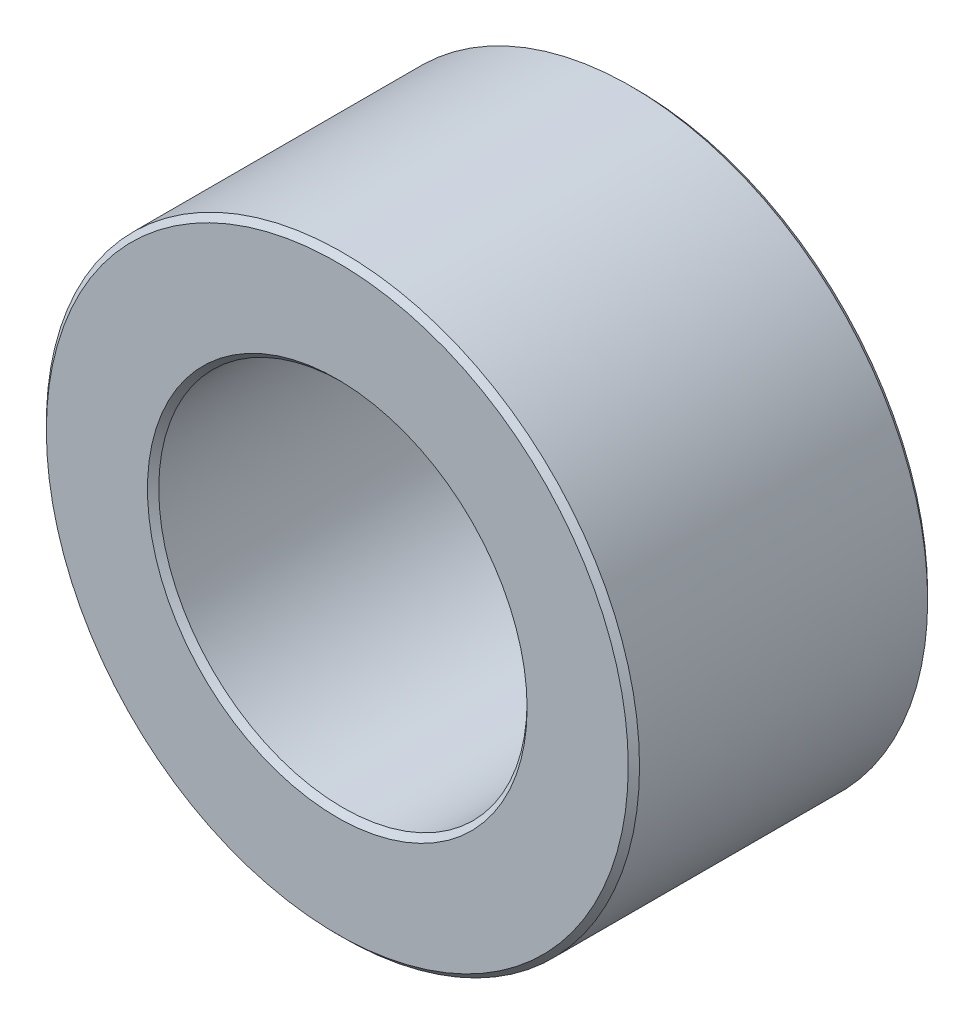
SolidWorks part; units mm, degrees
ref_plane "Front Plane" through (0, 0, 0) normal (0, 0, 1) x (1, 0, 0)
ref_plane "Top Plane" through (0, 0, 0) normal (0, 1, 0) x (1, 0, 0)
ref_plane "Right Plane" through (0, 0, 0) normal (1, 0, 0) x (0, 0, -1)
sketch "Sketch1" plane through (0, 0, 0) normal (0, 0, 1) x (1, 0, 0)
  circle A0 centre (0, 0) radius 52.5
  circle A1 centre (0, 0) radius 32.6
  dimension "D1" = 105
  dimension "D2" = 65.2
extrude "Boss-Extrude1" add sketch "Sketch1" along normal blind 53
chamfer "Chamfer1" distance 1 4 edges at (32.6, 0, 0) (32.6, 0, 53) (52.5, 0, 0) (52.5, 0, 53)
